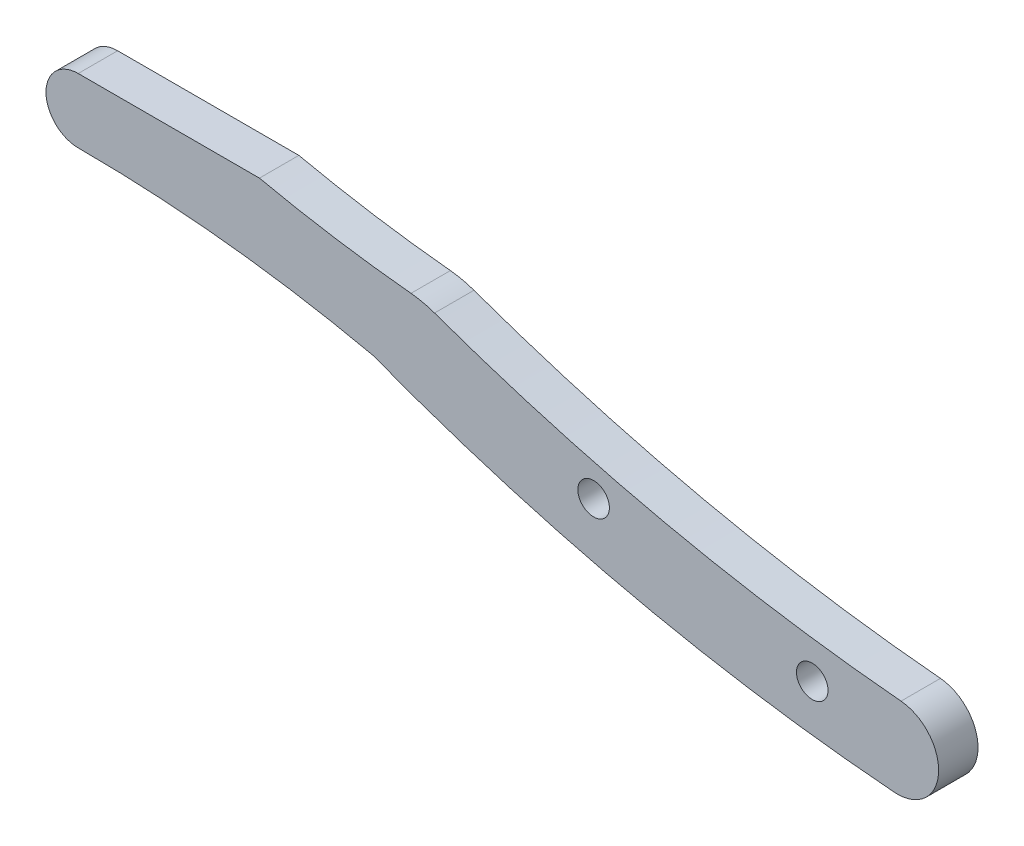
SolidWorks part; units mm, degrees
ref_plane "Front Plane" through (0, 0, 0) normal (0, 0, 1) x (1, 0, 0)
ref_plane "Top Plane" through (0, 0, 0) normal (0, 1, 0) x (1, 0, 0)
ref_plane "Right Plane" through (0, 0, 0) normal (1, 0, 0) x (0, 0, -1)
sketch "Sketch3" plane through (20.4945, 51.6288, -66.1729) normal (0, 0, 1) x (1, 0, 0)
  line L0 (-95, -38) -> (-60, -38) construction
  line L1 (-95, -35.45) -> (-76.6064, -35.45)
  arc A0 (-58.8338, -38.4225) -> (-11.481, -48.8616) centre (5.6197, 141.3251) ccw
  arc A1 (-11.481, -48.8616) -> (-12.1886, -57.2106) centre (-11.8562, -53.0343) cw
  arc A2 (-12.1886, -57.2106) -> (-65.1416, -45.2549) centre (2.9628, 133.1413) cw
  arc A3 (-61.2221, -37.8844) -> (-76.6064, -35.45) centre (-47.9795, 95.6296) cw
  arc A4 (-61.2221, -37.8844) -> (-58.8338, -38.4225) centre (-62.2091, -47.8356) cw
  arc A5 (-95, -35.45) -> (-95, -41.9928) centre (-95, -38.7214) ccw
  arc A6 (-95, -41.9928) -> (-65.1416, -45.2549) centre (-95, -180.2732) cw
  circle A7 centre (-42.6867, -46.6726) radius 1.6
  circle A8 centre (-20.4945, -51.6288) radius 1.6
  point P21 (0, 0)
  dimension "D1" = 35
  dimension "D4" = 10
  dimension "D14" = 7.3705
  dimension "D16" = 3.2
  dimension "D5" = 2.55
  dimension "D6" = 15.0343
  dimension "D7" = 48.1438
  dimension "D8" = 15.3843
  dimension "D9" = 2.4344
  dimension "D10" = 1.2221
  dimension "D11" = 2.3883
  dimension "D12" = 49.0334
  dimension "D13" = 3.9195
  dimension "D15" = 3.9928
  dimension "D17" = 18.5354
  dimension "D18" = 8.7881
  dimension "D19" = 4.9562
  dimension "D20" = 22.1922
extrude "Boss-Extrude1" add sketch "Sketch3" along normal blind 4
